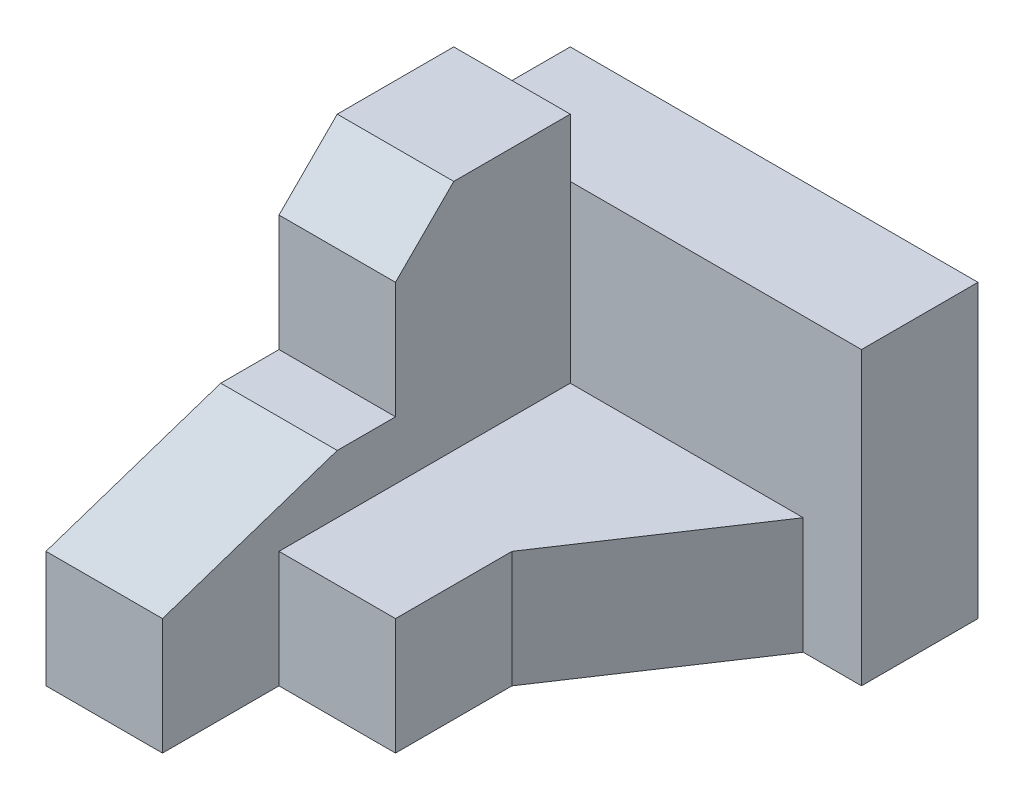
SolidWorks part; units mm, degrees
ref_plane "Front Plane" through (0, 0, 0) normal (0, 0, 1) x (1, 0, 0)
ref_plane "Top Plane" through (0, 0, 0) normal (0, 1, 0) x (1, 0, 0)
ref_plane "Right Plane" through (0, 0, 0) normal (1, 0, 0) x (0, 0, -1)
sketch "Sketch1" plane through (0, 0, 0) normal (0, 1, 0) x (1, 0, 0)
  line L0 (0, 0) -> (2, 0)
  line L1 (2, 0) -> (2, 2)
  line L2 (2, 2) -> (4, 2)
  line L3 (4, 2) -> (4, 4)
  line L4 (4, 4) -> (6, 7)
  line L5 (6, 7) -> (7, 7)
  line L6 (7, 7) -> (7, 9)
  line L7 (7, 9) -> (0, 9)
  line L8 (0, 9) -> (0, 0)
  dimension "D1" = 9
  dimension "D2" = 7
  dimension "D3" = 2
  dimension "D4" = 2
  dimension "D5" = 2
  dimension "D6" = 2
  dimension "D7" = 3
  dimension "D8" = 2
extrude "Boss-Extrude1" add sketch "Sketch1" along normal blind 2
sketch "Sketch2" plane through (0, 2, 0) normal (0, 1, 0) x (1, 0, 0)
  line L0 (7, 9) -> (0, 9)
  line L1 (0, 9) -> (0, 0)
  line L2 (0, 0) -> (2, 0)
  line L3 (2, 0) -> (2, 7)
  line L4 (2, 7) -> (7, 7)
  line L5 (7, 7) -> (7, 9)
extrude "Boss-Extrude2" add sketch "Sketch2" along normal blind 3
sketch "Sketch3" plane through (0, 5, 0) normal (0, 1, 0) x (1, 0, 0)
  line L0 (0, 9) -> (0, 0) construction
  line L1 (2, 7) -> (0, 7)
  line L2 (2, 7) -> (2, 4)
  line L3 (2, 4) -> (0, 4)
  line L4 (0, 7) -> (0, 4)
  dimension "D1" = 3
extrude "Boss-Extrude3" add sketch "Sketch3" along normal blind 1
sketch "Sketch4" plane through (2, 0, 0) normal (1, 0, 0) x (0, 0, -1)
  line L0 (5, 6) -> (4, 5)
  line L1 (4, 6) -> (7, 6) construction
  line L2 (4, 5) -> (4, 3)
  line L3 (4, 3) -> (3, 3)
  line L4 (3, 3) -> (0, 2)
  line L6 (0, 5) -> (0, 0) construction
  line L7 (0, 6) -> (5, 6)
  line L8 (5, 6) -> (4.9703, 6.0216)
  line L9 (0, 2) -> (0, 6)
  line M6 (7, 6) -> (4, 6)
  line M7 (4, 6) -> (4, 5)
  line M8 (4, 5) -> (0, 5)
  line M9 (0, 5) -> (0, 0)
  dimension "D1" = 1
  dimension "D2" = 2
  dimension "D3" = 1
  dimension "D4" = 4
extrude "Cut-Extrude1" cut sketch "Sketch4" against normal through all contours L0 M6 M7 | L4 L3 L2 M8 M9
